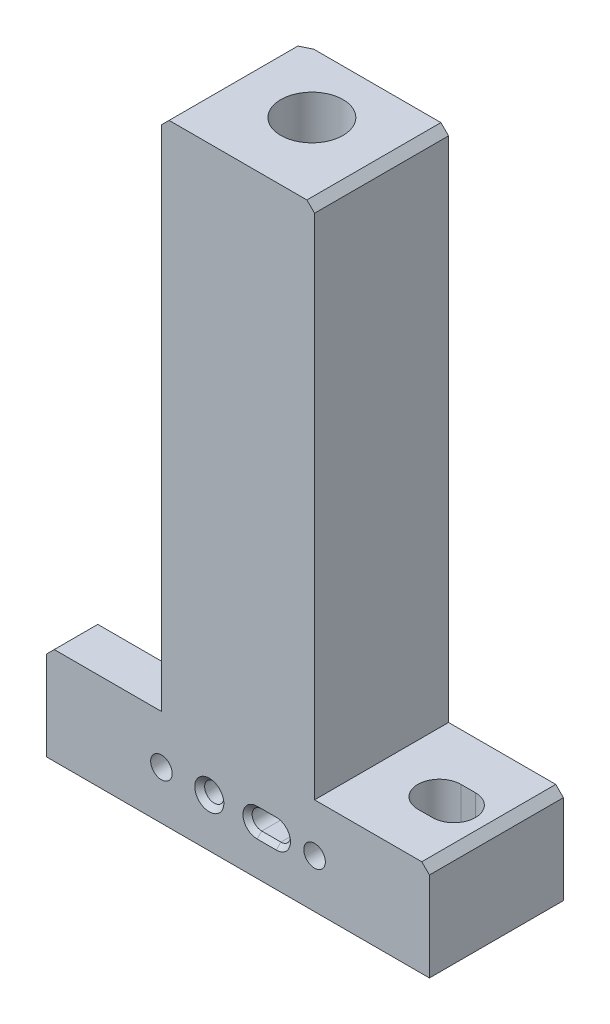
SolidWorks part; units mm, degrees
material "6061-T6 Al"
ref_plane "Front Plane" through (0, 0, 0) normal (0, 0, 1) x (1, 0, 0)
ref_plane "Top Plane" through (0, 0, 0) normal (0, 1, 0) x (1, 0, 0)
ref_plane "Right Plane" through (0, 0, 0) normal (1, 0, 0) x (0, 0, -1)
sketch "Sketch1" plane through (0, 0, 0) normal (0, 0, 1) x (1, 0, 0)
  line L0 (-63.5, 19.1623) -> (-25.4, 19.1623)
  line L1 (-63.5, 19.1623) -> (-63.5, -12.9687)
  line L2 (-63.5, -12.9687) -> (0, -12.9687)
  line L3 (0, -12.9687) -> (0, 190.2313)
  line L4 (0, 190.2313) -> (-25.4, 190.2313)
  line L5 (-25.4, 190.2313) -> (-25.4, 19.1623)
  dimension "D1" = 63.5
  dimension "D2" = 25.4
  dimension "D3" = 32.131
  dimension "D4" = 203.2
extrude "Extrude1" add sketch "Sketch1" along normal blind 44.45
mirror "Mirror2" about plane through (0, -12.9687, 44.45) normal (-1, 0, 0) of "Extrude1"
chamfer "Chamfer1" distance 2.54 angle 45 2 edges at (25.4, 190.2313, 22.225) (63.5, 19.1623, 22.225)
chamfer "Chamfer2" distance 2.54 angle 45 2 edges at (-63.5, 19.1623, 22.225) (-25.4, 190.2313, 22.225)
hole_wizard "13/16 (0.8125) Diameter Hole1" positions "3DSketch6" profile "Sketch13" hole size "13/16" standard "Ansi Inch"
sketch3d "3DSketch6"
  line L0 (22.86, 190.2313, 0) -> (-22.86, 190.2313, 0) construction
  line L3 (0, 190.2313, 19.939) -> (0, 190.2313, 0)
  point P0 (0, 190.2313, 19.939)
  dimension "D1" = 19.939
sketch "Sketch13" plane through (0, 190.2313, 19.939) normal (1, 0, 0) x (0, 0, 1)
  line L0 (0, 0) -> (0, 63.754)
  line L1 (0, 63.754) -> (10.3187, 63.754)
  line L2 (10.3187, 63.754) -> (10.3187, 0)
  line L5 (10.3187, 0) -> (0, 0)
  line L10 (0, 63.754) -> (-10.3188, 63.754) construction
  line L11 (0, -6.35) -> (0, 107.95) construction
  dimension "Hole Dia." = 20.6375
  dimension "Hole Depth" = 63.754
  dimension "Drill Angle" = 180
hole_wizard "#60 (0.04) Diameter Hole1" positions "Sketch18" profile "Sketch17" hole size "#60" standard "Ansi Inch"
sketch "Sketch18" plane through (0, 0, 0) normal (0, 0, -1) x (-1, 0, 0)
  line L0 (63.5, -12.9687) -> (-63.5, -12.9687) construction
  line L1 (25.4, 187.6913) -> (25.4, 19.1623) construction
  point P0 (0, 129.2713)
  dimension "D1" = 142.24
  dimension "D2" = 25.4
sketch "Sketch17" plane through (0, 129.2713, 0) normal (1, 0, 0) x (0, 1, 0)
  line L0 (0, 0) -> (0, 9.6203)
  line L1 (0, 9.6203) -> (0.508, 9.6203)
  line L2 (0.508, 9.6203) -> (0.508, 0)
  line L5 (0.508, 0) -> (0, 0)
  line L11 (0, -6.35) -> (0, 107.95) construction
  dimension "Thru Hole Dia." = 1.016
  dimension "Thru Hole Depth" = 9.6203
hole_wizard "CBORE for 1/4 Socket Head Cap Screw1" positions "3DSketch10" profile "Sketch19" counterbore size "1/4" standard "Ansi Inch" end condition through all
sketch3d "3DSketch10"
  line L0 (25.4, 19.1623, 0) -> (60.96, 19.1623, 0) construction
  line L1 (-25.4, 19.1623, 0) -> (-60.96, 19.1623, 0) construction
  line L2 (63.5, 16.6223, 0) -> (63.5, -12.9687, 0) construction
  line L3 (-63.5, 16.6223, 0) -> (-63.5, -12.9687, 0) construction
  point P0 (25.4, 3.0968, 0)
  point P2 (-25.4, 3.0968, 0)
  dimension "D1" = 16.0655
  dimension "D2" = 16.0655
  dimension "D3" = 38.1
  dimension "D4" = 38.1
sketch "Sketch19" plane through (25.4, 3.0968, 0) normal (1, 0, 0) x (0, 1, 0)
  line L0 (0, 0) -> (0, 44.45)
  line L1 (0, 44.45) -> (3.5712, 44.45)
  line L3 (3.5712, 44.45) -> (3.5712, 15.748)
  line L4 (3.5712, 15.748) -> (5.5562, 15.748)
  line L5 (5.5562, 15.748) -> (5.5562, 0)
  line L7 (5.5562, 0) -> (0, 0)
  line L11 (0, -6.35) -> (0, 107.95) construction
  dimension "Thru Hole Dia." = 7.1425
  dimension "Thru Hole Depth" = 44.45
  dimension "C'Bore Dia." = 11.1125
  dimension "C'Bore Depth" = 15.748
hole_wizard "1/4 (0.25) Diameter Hole2" positions "Sketch21" profile "Sketch20" hole size "1/4" standard "Ansi Inch"
sketch "Sketch21" plane through (0, 0, 44.45) normal (0, 0, 1) x (1, 0, 0)
  line L0 (-63.5, -12.9687) -> (63.5, -12.9687) construction
  line L1 (-63.5, 16.6223) -> (-63.5, -12.9687) construction
  point P0 (-9.525, 3.0968)
  dimension "D1" = 16.0655
  dimension "D2" = 53.975
sketch "Sketch20" plane through (-9.525, 3.0968, 44.45) normal (1, 0, 0) x (0, -1, 0)
  line L0 (0, 0) -> (0, 14.6131)
  line L1 (0, 14.6131) -> (3.1839, 12.7)
  line L2 (3.1839, 12.7) -> (3.1839, 1.6421)
  line L3 (3.1839, 1.6421) -> (4.826, 0)
  line L5 (4.826, 0) -> (0, 0)
  line L6 (-3.1839, 1.6421) -> (-4.826, 0) construction
  line L10 (0, 14.6131) -> (-3.1839, 12.7) construction
  line L11 (0, -6.35) -> (0, 107.95) construction
  dimension "Hole Dia." = 6.3678
  dimension "Hole Depth" = 12.7
  dimension "Near C'Sink Dia." = 9.652
  dimension "Near C'Sink Angle" = 90
  dimension "Drill Angle" = 118
sketch "Sketch22" plane through (0, 0, 44.45) normal (0, 0, 1) x (1, 0, 0)
  line L0 (12.7, 3.0968) -> (6.35, 3.0968) construction
  line L1 (12.7, -0.087) -> (6.35, -0.087)
  line L2 (12.7, 6.2807) -> (6.35, 6.2807)
  line L3 (63.5, 16.6223) -> (63.5, -12.9687) construction
  line L5 (-9.525, 3.0968) -> (6.35, 3.0968) construction
  arc A0 (12.7, -0.087) -> (12.7, 6.2807) centre (12.7, 3.0968) ccw
  arc A1 (6.35, 6.2807) -> (6.35, -0.087) centre (6.35, 3.0968) ccw
  circle A2 centre (-9.525, 3.0968) radius 3.1839 construction
  point P2 (9.525, 3.0968)
  dimension "D2" = 6.35
  dimension "D3" = 53.975
extrude "Extrude4" cut sketch "Sketch22" against normal blind 12.7
hole_wizard "1/2-20 Tapped Hole3" positions "Sketch26" profile "Sketch25" tap size "1/2-20" standard "Ansi Inch"
sketch "Sketch26" plane through (0, 126.4773, 0) normal (0, 1, 0) x (-1, 0, 0)
  circle A0 centre (0, 19.939) radius 10.3187 construction
  point P0 (0, 19.939)
sketch "Sketch25" plane through (0, 126.4773, 19.939) normal (1, 0, 0) x (0, 0, 1)
  line L0 (0, 0) -> (0, 85.8723)
  line L1 (0, 85.8723) -> (5.7544, 82.55)
  line L2 (5.7544, 82.55) -> (5.7544, 0)
  line L5 (5.7544, 0) -> (0, 0)
  line L10 (0, 85.8723) -> (-5.7544, 82.55) construction
  line L11 (0, -6.35) -> (0, 107.95) construction
  dimension "Tap Drill Dia." = 11.5087
  dimension "Tap Drill Depth" = 82.55
  dimension "Drill Angle" = 120
cosmetic thread "Hole Thread4" parameters "D1"=70.866, "D2"=12.7
sketch "Sketch27" plane through (0, 19.1623, 0) normal (0, 1, 0) x (1, 0, 0)
  line L1 (-19.3381, 0) -> (-63.5, -21.5392)
  line L2 (-25.4, 0) -> (-60.96, 0) construction
  line L3 (-19.3381, 0) -> (-63.5, 0)
  line L5 (-63.5, -21.5392) -> (-63.5, 0)
  dimension "D1" = 26
  dimension "D2" = 63.5
  dimension "D3" = 21.5392
extrude "Extrude5" cut sketch "Sketch27" against normal blind 33.02 and the other way through all
chamfer "Chamfer3" distance 1.524 angle 45 4 edges at (15.8839, 3.0968, 44.45) (9.525, 6.2807, 44.45) (9.525, -0.087, 44.45) (3.1661, 3.0968, 44.45)
sketch "Sketch28" plane through (0, 19.1623, 0) normal (0, 1, 0) x (1, 0, 0)
  line L0 (45.212, -22.86) -> (50.038, -22.86) construction
  line L1 (45.212, -15.7226) -> (50.038, -15.7226)
  line L2 (45.212, -29.9974) -> (50.038, -29.9974)
  line L3 (45.212, -22.86) -> (-38.227, -22.86) construction
  line L4 (-38.227, -22.86) -> (-63.627, -22.86) construction
  line L5 (-38.227, -29.9974) -> (-63.627, -29.9974)
  line L6 (-38.227, -15.7226) -> (-63.627, -15.7226)
  line L7 (25.4, -44.45) -> (60.96, -44.45) construction
  arc A0 (45.212, -15.7226) -> (45.212, -29.9974) centre (45.212, -22.86) ccw
  arc A1 (50.038, -29.9974) -> (50.038, -15.7226) centre (50.038, -22.86) ccw
  circle A2 centre (0, -19.939) radius 5.7544 construction
  arc A3 (-38.227, -29.9974) -> (-38.227, -15.7226) centre (-38.227, -22.86) ccw
  arc A4 (-63.627, -15.7226) -> (-63.627, -29.9974) centre (-63.627, -22.86) ccw
  point P2 (47.625, -22.86)
  point P14 (-50.927, -22.86)
  dimension "D1" = 47.625
  dimension "D2" = 7.1374
  dimension "D3" = 4.826
  dimension "D4" = 85.852
  dimension "D5" = 25.4
  dimension "D6" = 21.59
extrude "Extrude6" cut sketch "Sketch28" against normal through all
sketch "Sketch29" plane through (0, 19.1623, 0) normal (0, 1, 0) x (1, 0, 0)
  line L0 (-51.5742, -15.7226) -> (-50.0502, -14.9793)
  line L1 (-50.0502, -14.9793) -> (-50.0502, -15.7226)
  line L2 (-51.5742, -15.7226) -> (-50.0502, -15.7226)
  line L4 (-51.5742, -15.7226) -> (-25.4, -2.9566) construction
  dimension "D1" = 1.524
extrude "Cut-Extrude1" cut sketch "Sketch29" against normal through all
